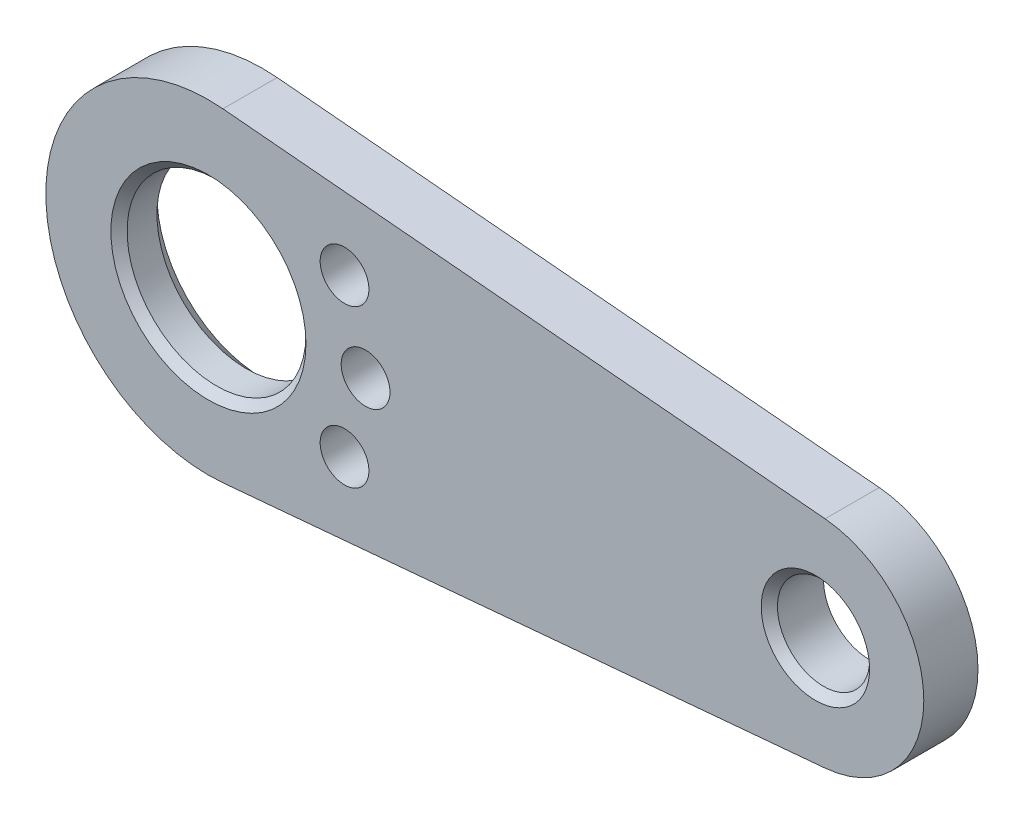
SolidWorks part; units mm, degrees
ref_plane "Front Plane" through (0, 0, 0) normal (0, 0, 1) x (1, 0, 0)
ref_plane "Top Plane" through (0, 0, 0) normal (0, 1, 0) x (1, 0, 0)
ref_plane "Right Plane" through (0, 0, 0) normal (1, 0, 0) x (0, 0, -1)
sketch "Sketch1" plane through (0, 0, 0) normal (0, 0, 1) x (1, 0, 0)
  line L0 (0.2679, 2.988) -> (11.3786, 1.992)
  line L1 (0, 0) -> (11.2, 0) construction
  line L2 (0.2679, -2.988) -> (11.3786, -1.992)
  arc A0 (0.2679, 2.988) -> (0.2679, -2.988) centre (0, 0) ccw
  arc A1 (11.3786, -1.992) -> (11.3786, 1.992) centre (11.2, 0) ccw
  dimension "D1" = 3
  dimension "D2" = 2
  dimension "D3" = 11.2
extrude "Boss-Extrude1" add sketch "Sketch1" against normal blind 1
sketch "Sketch2" plane through (0, 0, 0) normal (0, 0, 1) x (1, 0, 0)
  circle A0 centre (0, 0) radius 1.65
  circle A1 centre (11.2, 0) radius 0.85
  dimension "D1" = 3.3
  dimension "D2" = 1.7
extrude "Cut-Extrude1" cut sketch "Sketch2" against normal through all
chamfer "Chamfer1" distance 0.15 angle 45 2 edges at (1.65, 0, 0) (12.05, 0, 0)
chamfer "Chamfer2" distance 0.3 angle 45 1 edges at (1.65, 0, -1)
hole_wizard "Ø0.9 (0.9) Diameter Hole1" positions "Sketch4" profile "Sketch3" hole size "Ø0.9" standard "DIN" end condition up to next
sketch "Sketch4" plane through (0, 0, 0) normal (0, 0, 1) x (1, 0, 0)
  line L0 (0, 0) -> (2.9, 0) construction
  line L1 (0, 0) -> (2.5115, 1.45) construction
  line L2 (0, 0) -> (2.5115, -1.45) construction
  circle A0 centre (0, 0) radius 2.9 construction
  point P6 (2.9, 0)
  point P8 (2.5115, 1.45)
  point P10 (2.5115, -1.45)
  dimension "D1" = 5.8
  dimension "D2" = 30
  dimension "D3" = 30
sketch "Sketch3" plane through (2.9, 0, 0) normal (1, 0, 0) x (0, -1, 0)
  line L0 (0, 0) -> (0, 1)
  line L1 (0, 1) -> (0.45, 1)
  line L2 (0.45, 1) -> (0.45, 0)
  line L5 (0.45, 0) -> (0, 0)
  line L11 (0, -6.35) -> (0, 107.95) construction
  dimension "Thru Hole Dia." = 0.9
  dimension "Thru Hole Depth" = 1
